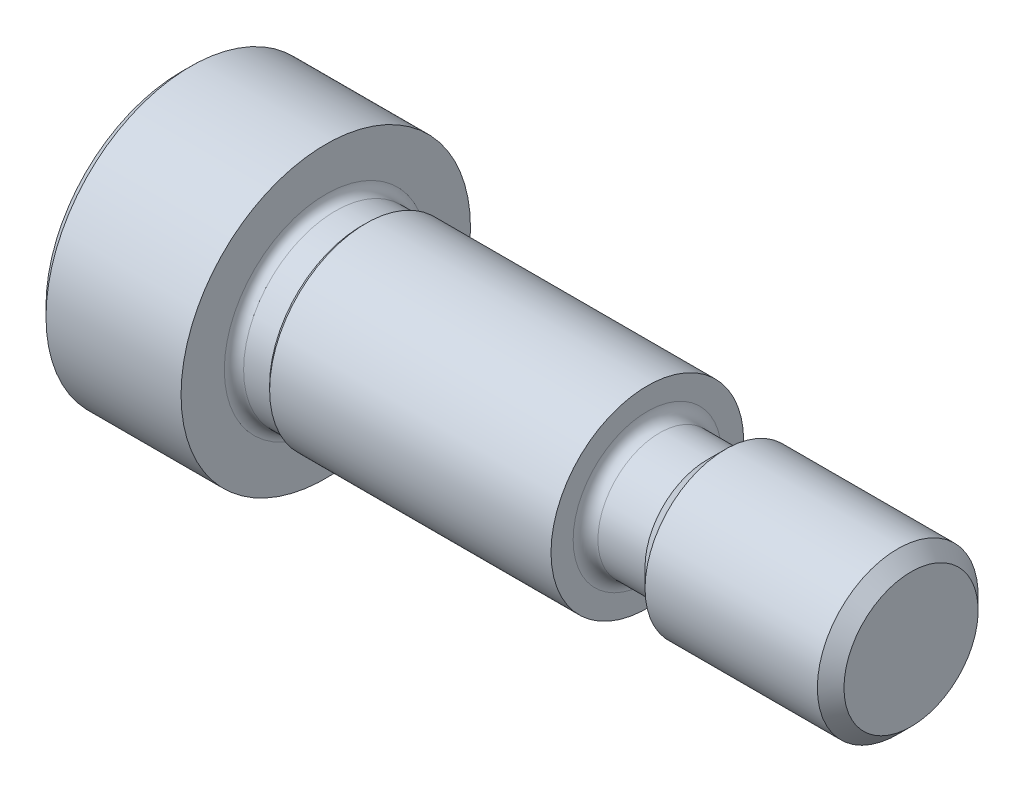
SolidWorks part; units mm, degrees
ref_plane "Plane1" through (0, 0, 0) normal (0, 0, 1) x (1, 0, 0)
ref_plane "Plane2" through (0, 0, 0) normal (0, 1, 0) x (1, 0, 0)
ref_plane "Plane3" through (0, 0, 0) normal (1, 0, 0) x (0, 0, -1)
sketch "BodySke" plane through (0, 0, 0) normal (0, 0, 1) x (1, 0, 0)
  line L0 (0, 0) -> (0, 9)
  line L2 (0, 9) -> (9, 9)
  line L3 (9, 9) -> (9, 6.31)
  line L4 (9.6, 5.71) -> (11.218, 5.71)
  line L5 (11.218, 5.71) -> (11.5, 5.992)
  line L6 (11.5, 5.992) -> (29, 5.992)
  line L7 (29, 5.992) -> (29, 4.615)
  line L8 (29.77, 3.845) -> (32.7, 3.845)
  line L9 (32.7, 3.845) -> (33.855, 5)
  line L10 (33.855, 5) -> (44.572, 5)
  line L11 (44.572, 5) -> (45.4, 4.172)
  line L12 (45.4, 4.172) -> (45.4, 0)
  line L13 (45.4, 0) -> (0, 0)
  line L14 (-6.35, 0) -> (107.95, 0) construction
  line L15 (44.572, -5) -> (45.4, -4.172) construction
  line L16 (29, -3.845) -> (32.7, -3.845) construction
  line L17 (11.5, -5.992) -> (29, -5.992) construction
  line L18 (9, -5.71) -> (11.218, -5.71) construction
  line L20 (34.2, 8.6964) -> (34.2, -8.6564) construction
  line L21 (29, 7.9481) -> (29, -7.9015) construction
  arc A0 (29, 4.615) -> (29.77, 3.845) centre (29.77, 4.615) ccw
  arc A1 (9.6, 5.71) -> (9, 6.31) centre (9.6, 6.31) cw
  point P29 (29, 3.845)
  point P32 (9, 5.71)
  dimension "Thread_ch_ang" = 45
  dimension "D11" = 45
  dimension "D13" = 45
  dimension "Shoulder_neck_width" = 2.5
revolve "BaseBody" add sketch "BodySke" angle 360 about L14
cosmetic thread "ThreadCosmetic" parameters "Thread_length"=11.2, "Thread_minor"=8.344
chamfer "Chamfer1" distance 0.6 1 edges at (0, 0, 9)
sketch "Sketch2" plane through (0, 0, 0) normal (0, 0, 1) x (1, 0, 0)
  line L0 (0, 3.0475) -> (4.9, 3.0475)
  line L1 (4.9, 3.0475) -> (6.6595, 0)
  line L3 (6.6595, 0) -> (0, 0)
  line L4 (0, 0) -> (0, 3.0475)
  line L5 (0, -3.0475) -> (4.9, -3.0475) construction
  line L6 (0, 0) -> (47.625, 0) construction
  dimension "D2" = 60
  dimension "PreBroach_depth" = 4.9
  dimension "PreBroach_dia" = 6.095
revolve "PreBroach" cut sketch "Sketch2" angle 360 about L6
sketch "Sketch3" plane through (0, 0, 0) normal (-1, 0, 0) x (0, 0, 1)
  line L0 (-3.0475, -1.7595) -> (-3.0475, 1.7595)
  line L1 (-3.0475, 1.7595) -> (0, 3.5189)
  line L2 (0, 3.5189) -> (3.0475, 1.7595)
  line L3 (3.0475, 1.7595) -> (3.0475, -1.7595)
  line L4 (3.0475, -1.7595) -> (0, -3.5189)
  line L5 (0, -3.5189) -> (-3.0475, -1.7595)
  dimension "D3" = 120
extrude "Hex" cut sketch "Sketch3" against normal blind 4.9
sketch "ThdSchSke" plane through (0, 0, 0) normal (0, 0, 1) x (1, 0, 0)
  line L0 (34.2, -4.172) -> (32.9256, -5.992)
  line L1 (34.2, -4.172) -> (35.4744, -5.992)
  line L2 (35.4744, -5.992) -> (35.4744, -7.49)
  line L3 (-3.175, 0) -> (5.1513, 0) construction
  line L5 (35.4744, -7.49) -> (32.9256, -7.49)
  line L6 (32.9256, -7.49) -> (32.9256, -5.992)
  dimension "SideAngle" = 55
  dimension "VeeAngle" = 70
revolve "ThreadSchematic" [suppressed] cut sketch "ThdSchSke" angle 360 about L3
pattern_linear "ThdSchPat" [suppressed]
equation "\"Thread_minor@ThreadCosmetic\" = \"Minor_dia@BodySke\""
equation "\"D1@Sketch3\" = \"Hex_size@Sketch3\" / 2"
equation "\"D2@Sketch3\" = \"D1@Sketch3\""
equation "\"D4@Sketch3\" = \"Hex_size@Sketch3\""
equation "\"Width@Chamfer1\" = \"Head_fillet_radius@BodySke\""
equation "\"Thread_length@ThreadCosmetic\" = ((sgn( (\"Thread_length@BodySke\" - \"Advance@BodySke\" - \"Thread_neck_width@BodySke\" ) - \"Thread_nom@BodySke\" )-1)*( (\"Thread_length@BodySke\" - \"Advance@BodySke\" - \"Thread_neck_width@BodySke\" ) - \"Thread_nom@BodySke\" ))/-2+ \"Thread_nom@BodySke\""
equation "\"Thread_minor@ThdSchSke\" = \"Minor_dia@BodySke\""
equation "\"Diameter@ThdSchSke\" = \"Diameter@BodySke\""
equation "\"Overcut@ThdSchSke\" = \"Diameter@BodySke\" * 1.25"
equation "\"Start@ThdSchSke\" = \"Head_ht@BodySke\" + \"Length@BodySke\" + \"Thread_length@BodySke\" -  \"Thread_length@ThreadCosmetic\"  '---Non-countersunk---"
equation "\"Num_threads@ThdSchPat\" = int( \"Thread_length@ThreadCosmetic\" / \"Advance@BodySke\" + 0.999 ) + 1"
equation "\"Advance@ThdSchPat\" = \"Thread_length@ThreadCosmetic\" /  (\"Num_threads@ThdSchPat\" - 1) 'relax it"
equation "\"Num_threads@ThdSchPat\" = \"Num_threads@ThdSchPat\" - sgn( \"Num_threads@ThdSchPat\" - 1) '---chamfered tips only---"
